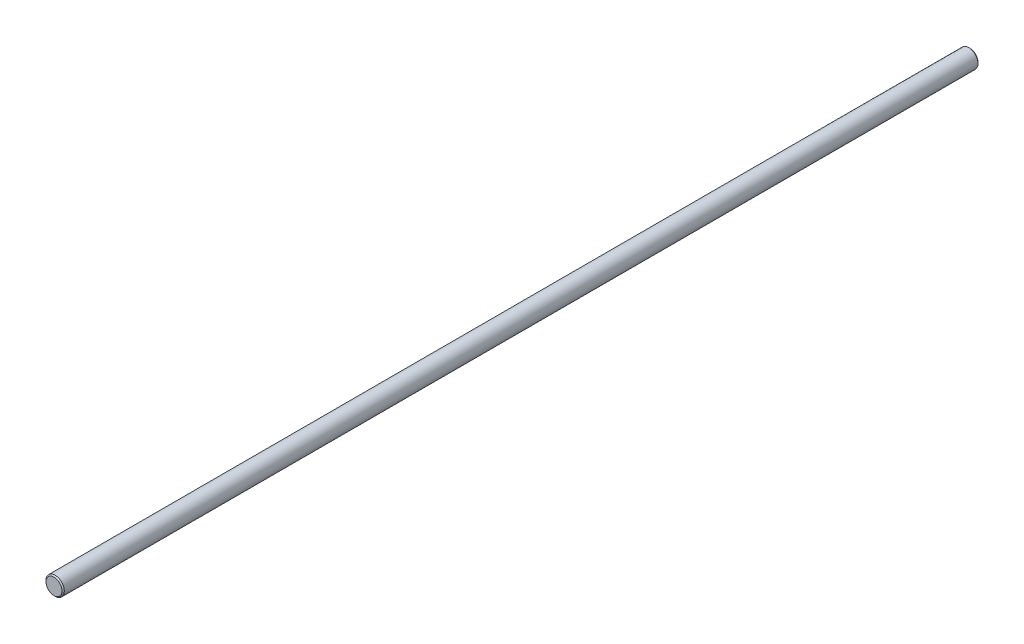
SolidWorks part; units mm, degrees
ref_plane "Plan de face" through (0, 0, 0) normal (0, 0, 1) x (1, 0, 0)
ref_plane "Plan de dessus" through (0, 0, 0) normal (0, 1, 0) x (1, 0, 0)
ref_plane "Plan de droite" through (0, 0, 0) normal (1, 0, 0) x (0, 0, -1)
sketch "Esquisse1" plane through (0, 0, 0) normal (0, 0, 1) x (1, 0, 0)
  circle A0 centre (0, 0) radius 4
  dimension "D1" = 8
extrude "Boss.-Extru.1" add sketch "Esquisse1" along normal blind 400
chamfer "Chanfrein1" distance 0.5 angle 45 2 edges at (4, 0, 400) (4, 0, 0)
